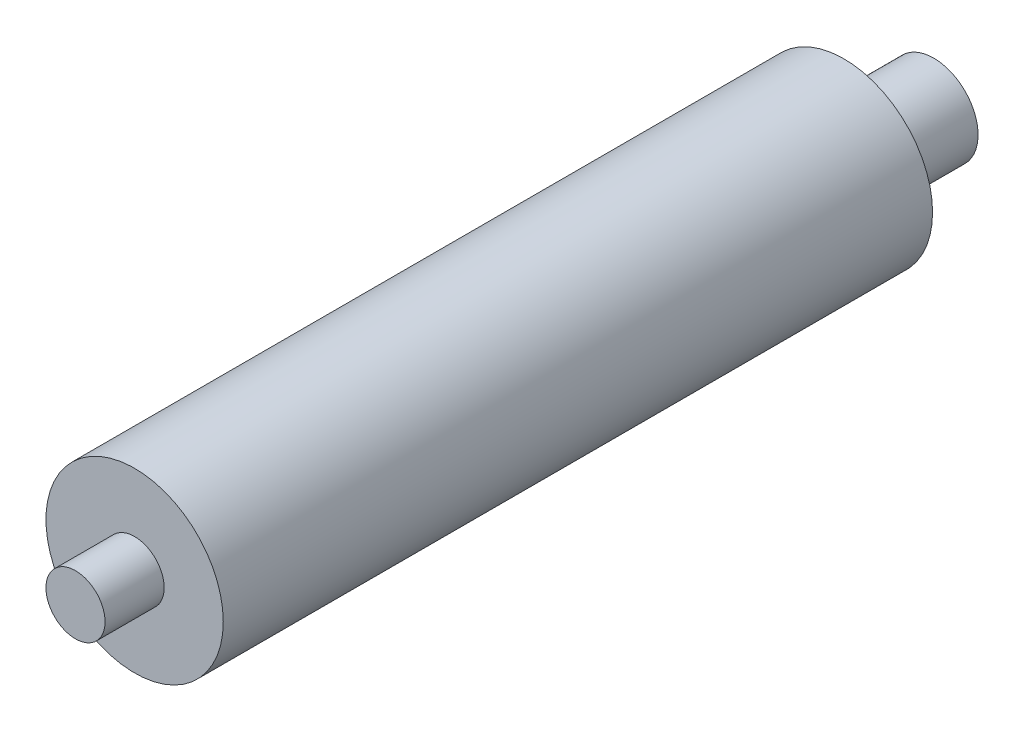
SolidWorks part; units mm, degrees
ref_plane "Front Plane" through (0, 0, 0) normal (0, 0, 1) x (1, 0, 0)
ref_plane "Top Plane" through (0, 0, 0) normal (0, 1, 0) x (1, 0, 0)
ref_plane "Right Plane" through (0, 0, 0) normal (1, 0, 0) x (0, 0, -1)
sketch "Sketch1" plane through (0, 0, 0) normal (0, 0, 1) x (1, 0, 0)
  circle A0 centre (0, 0) radius 9.525
  dimension "D1" = 19.05
extrude "Boss-Extrude1" add sketch "Sketch1" along normal blind 76.2
sketch "Sketch2" plane through (0, 0, 76.2) normal (0, 0, 1) x (1, 0, 0)
  circle A0 centre (0, 0) radius 3.175
  dimension "D1" = 6.35
extrude "Boss-Extrude2" add sketch "Sketch2" along normal blind 6.35
sketch "Sketch3" plane through (0, 0, 0) normal (0, 0, -1) x (-1, 0, 0)
  circle A0 centre (0, 0) radius 4.7625
  dimension "D1" = 9.525
extrude "Boss-Extrude3" add sketch "Sketch3" along normal blind 9.652
